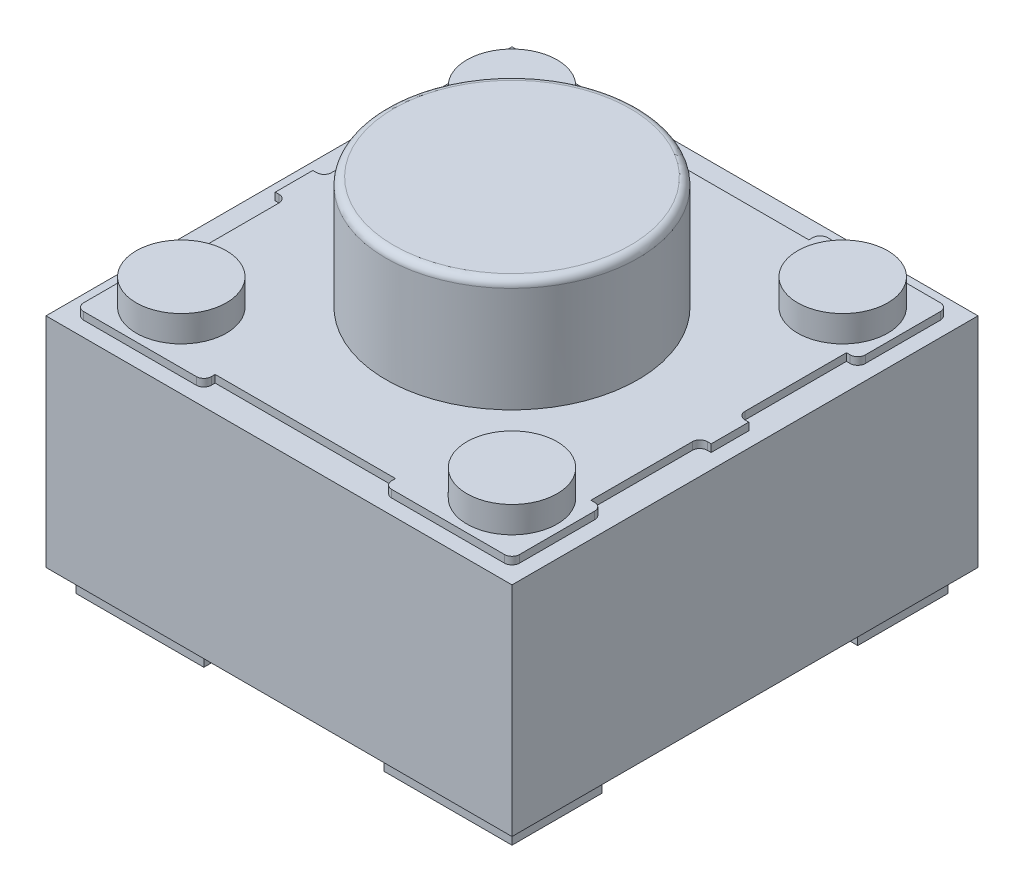
SolidWorks part; units mm, degrees
ref_plane "Plan de face" through (0, 0, 0) normal (0, 0, 1) x (1, 0, 0)
ref_plane "Plan de dessus" through (0, 0, 0) normal (0, 1, 0) x (1, 0, 0)
ref_plane "Plan de droite" through (0, 0, 0) normal (1, 0, 0) x (0, 0, -1)
sketch "Esquisse1" plane through (0, 0, 0) normal (0, 1, 0) x (1, 0, 0)
  line L2 (0, 0) -> (0, 6.2)
  line L3 (0, 6.2) -> (6.2, 6.2)
  line L4 (6.2, 0) -> (6.2, 6.2)
  line L5 (0.2, 0.2) -> (1.9, 0.2)
  line L6 (0.2, 0.2) -> (0.2, 1.4)
  line L7 (0.2, 1.4) -> (1.9, 1.4)
  line L8 (1.9, 0.2) -> (1.9, 1.4)
  line L9 (0.2, 6) -> (1.9, 6)
  line L10 (0.2, 6) -> (0.2, 4.8)
  line L11 (0.2, 4.8) -> (1.9, 4.8)
  line L12 (1.9, 6) -> (1.9, 4.8)
  line L13 (6, 6) -> (4.3, 6)
  line L14 (6, 6) -> (6, 4.8)
  line L15 (6, 4.8) -> (4.3, 4.8)
  line L16 (4.3, 6) -> (4.3, 4.8)
  line L17 (6, 0.2) -> (4.3, 0.2)
  line L18 (6, 0.2) -> (6, 1.4)
  line L19 (6, 1.4) -> (4.3, 1.4)
  line L20 (4.3, 0.2) -> (4.3, 1.4)
  dimension "D1" = 6.2
  dimension "D2" = 6.2
  dimension "D3" = 0.2
  dimension "D6" = 0.2
  dimension "D7" = 0.2
  dimension "D8" = 0.2
  dimension "D9" = 0.2
  dimension "D10" = 0.2
  dimension "D11" = 1.7
  dimension "D12" = 1.2
extrude "Boss.-Extru.1" add sketch "Esquisse1" along normal blind 0.3 contours L12 L9 L10 L11 | L5 L8 L7 L6 | L20 L17 L18 L19 | L13 L16 L15 L14
sketch "Esquisse2" plane through (0, 0.3, 0) normal (0, 1, 0) x (1, 0, 0)
  line L1 (0, 0) -> (6.2, 0)
  line L2 (0, 0) -> (0, 6.2)
  line L3 (0, 6.2) -> (6.2, 6.2)
  line L4 (6.2, 0) -> (6.2, 6.2)
  dimension "D1" = 6.2
  dimension "D2" = 6.2
extrude "Boss.-Extru.2" add sketch "Esquisse2" along normal blind 3
sketch "Esquisse3" plane through (0, 3.3, 0) normal (0, 1, 0) x (1, 0, 0)
  line L0 (0, 0) -> (0, 6.2) construction
  line L1 (0, 6.2) -> (6.2, 6.2) construction
  line L2 (6.2, 0) -> (6.2, 6.2) construction
  line L3 (0, 0) -> (0, 6.2)
  line L4 (1.9, 6) -> (0.2, 6)
  line L5 (1.9, 4.8) -> (1.9, 6)
  line L6 (0.2, 4.8) -> (1.9, 4.8)
  line L7 (0.2, 6) -> (0.2, 4.8)
  line L8 (1.8, 6) -> (0.3, 6)
  line L9 (1.9, 5.85) -> (1.9, 5.9)
  line L10 (0.3, 4.8) -> (0.35, 4.8)
  line L11 (0.2, 5.9) -> (0.2, 4.9)
  line L12 (0.2, 0.2) -> (1.9, 0.2)
  line L13 (1.9, 0.2) -> (1.9, 1.4)
  line L14 (1.9, 1.4) -> (0.2, 1.4)
  line L15 (0.2, 1.4) -> (0.2, 0.2)
  line L16 (0.3, 0.2) -> (1.8, 0.2)
  line L17 (1.9, 0.3) -> (1.9, 0.35)
  line L18 (0.35, 1.4) -> (0.3, 1.4)
  line L19 (0.2, 1.3) -> (0.2, 0.3)
  line L20 (4.3, 0.2) -> (6, 0.2)
  line L21 (4.3, 1.4) -> (4.3, 0.2)
  line L22 (6, 1.4) -> (4.3, 1.4)
  line L23 (6, 0.2) -> (6, 1.4)
  line L24 (4.4, 0.2) -> (5.9, 0.2)
  line L25 (4.3, 0.35) -> (4.3, 0.3)
  line L26 (5.9, 1.4) -> (5.85, 1.4)
  line L27 (6, 0.3) -> (6, 1.3)
  line L28 (6, 6) -> (4.3, 6)
  line L29 (6, 4.8) -> (6, 6)
  line L30 (4.3, 4.8) -> (6, 4.8)
  line L31 (4.3, 6) -> (4.3, 4.8)
  line L32 (5.9, 6) -> (4.4, 6)
  line L33 (6, 4.9) -> (6, 5.9)
  line L34 (5.85, 4.8) -> (5.9, 4.8)
  line L35 (4.3, 5.9) -> (4.3, 5.85)
  line L36 (0, 6.2) -> (6.2, 6.2)
  line L37 (6.2, 0) -> (6.2, 6.2)
  line L38 (1.9, 0.35) -> (4.3, 0.35)
  line L39 (1.9, 5.85) -> (4.3, 5.85)
  line L40 (0.2, 3.35) -> (0.2, 2.85)
  line L41 (6, 3.35) -> (6, 2.85)
  line L42 (0.2, 2.85) -> (0.25, 2.85)
  line L43 (0.2, 3.35) -> (0.25, 3.35)
  line L44 (0.35, 3.45) -> (0.35, 4.8)
  line L45 (0.35, 2.75) -> (0.35, 1.4)
  line L46 (6, 2.85) -> (5.95, 2.85)
  line L47 (5.85, 2.75) -> (5.85, 1.4)
  line L48 (6, 3.35) -> (5.95, 3.35)
  line L49 (5.85, 3.45) -> (5.85, 4.8)
  line L50 (6, 3.1) -> (0.2, 3.1) construction
  line L51 (3.1, 6.2) -> (3.1, 0) construction
  line L52 (0, 0) -> (6.2, 0) construction
  arc A0 (5.95, 2.85) -> (5.85, 2.75) centre (5.95, 2.75) ccw
  arc A1 (5.95, 3.35) -> (5.85, 3.45) centre (5.95, 3.45) cw
  arc A2 (0.25, 3.35) -> (0.35, 3.45) centre (0.25, 3.45) ccw
  arc A3 (0.25, 2.85) -> (0.35, 2.75) centre (0.25, 2.75) cw
  arc A4 (6, 4.9) -> (5.9, 4.8) centre (5.9, 4.9) cw
  arc A5 (5.9, 6) -> (6, 5.9) centre (5.9, 5.9) cw
  arc A6 (4.4, 6) -> (4.3, 5.9) centre (4.4, 5.9) ccw
  arc A7 (1.8, 6) -> (1.9, 5.9) centre (1.8, 5.9) cw
  arc A8 (0.3, 6) -> (0.2, 5.9) centre (0.3, 5.9) ccw
  arc A9 (0.3, 4.8) -> (0.2, 4.9) centre (0.3, 4.9) cw
  arc A10 (0.3, 1.4) -> (0.2, 1.3) centre (0.3, 1.3) ccw
  arc A11 (5.9, 1.4) -> (6, 1.3) centre (5.9, 1.3) cw
  arc A12 (5.9, 0.2) -> (6, 0.3) centre (5.9, 0.3) ccw
  arc A13 (4.4, 0.2) -> (4.3, 0.3) centre (4.4, 0.3) cw
  arc A14 (1.8, 0.2) -> (1.9, 0.3) centre (1.8, 0.3) ccw
  arc A15 (0.3, 0.2) -> (0.2, 0.3) centre (0.3, 0.3) cw
  point P38 (3.1, 3.1)
  point P43 (3.1, 3.1)
  line M17 (0, 6.2) -> (0, 0)
  line M18 (0, 0) -> (6.2, 0)
  line M19 (6.2, 0) -> (6.2, 6.2)
  line M20 (6.2, 6.2) -> (0, 6.2)
  dimension "D5" = 0.1
  dimension "D6" = 0.5
  dimension "D7" = 0.05
  dimension "D8" = 0.05
  dimension "D1" = 0
  dimension "D2" = 0
  dimension "D3" = 0
  dimension "D4" = 0
extrude "Enlèv. mat.-Extru.1" cut sketch "Esquisse3" against normal blind 0.1 contours L16 A15 L19 A10 L18 L45 A3 L42 L40 L43 A2 L44 L10 A9 L11 A8 L8 A7 L9 L39 L35 A6 L32 A5 L33 A4 L34 L49 A1 L48 L41 L46 A0 L47 L26 A11 L27 A12 L24 A13 L25 L38 L17 A14 M20 M17 M18 M19
sketch "Esquisse4" plane through (0, 3.3, 0) normal (0, 1, 0) x (1, 0, 0)
  line L0 (3.1, 6.2) -> (3.1, 0) construction
  line L1 (6.2, 6.2) -> (0, 6.2) construction
  line L2 (0, 0) -> (6.2, 0) construction
  line L3 (0, 0.9) -> (6.2, 0.9) construction
  line L4 (0, 6.2) -> (0, 0) construction
  line L5 (0, 3.1) -> (6.2, 3.1) construction
  line L6 (6.2, 0) -> (6.2, 6.2) construction
  line L7 (6.2, 5.3) -> (0, 5.3) construction
  line L8 (5.3, 6.2) -> (5.3, 0) construction
  line L9 (0.9, 6.2) -> (0.9, 0) construction
  circle A0 centre (0.9, 5.3) radius 0.6
  circle A1 centre (5.3, 5.3) radius 0.6
  circle A2 centre (0.9, 0.9) radius 0.6
  circle A3 centre (5.3, 0.9) radius 0.6
  point P20 (0.9, 5.3)
  point P21 (5.3, 5.3)
  point P22 (5.3, 0.9)
  point P23 (0.9, 0.9)
  dimension "D4" = 1.2
  dimension "D1" = 0.9
  dimension "D2" = 0.9
  dimension "D3" = 0.9
  dimension "D5" = 0.9
extrude "Boss.-Extru.3" add sketch "Esquisse4" along normal blind 0.35
sketch "Esquisse5" plane through (0, 3.3, 0) normal (0, 1, 0) x (1, 0, 0)
  circle A0 centre (3.1, 3.1) radius 1.675
  dimension "D1" = 3.35
extrude "Boss.-Extru.4" add sketch "Esquisse5" along normal blind 1.5
fillet "Congé1" radius 0.1 1 edges at (3.1, 4.8, -1.425)
